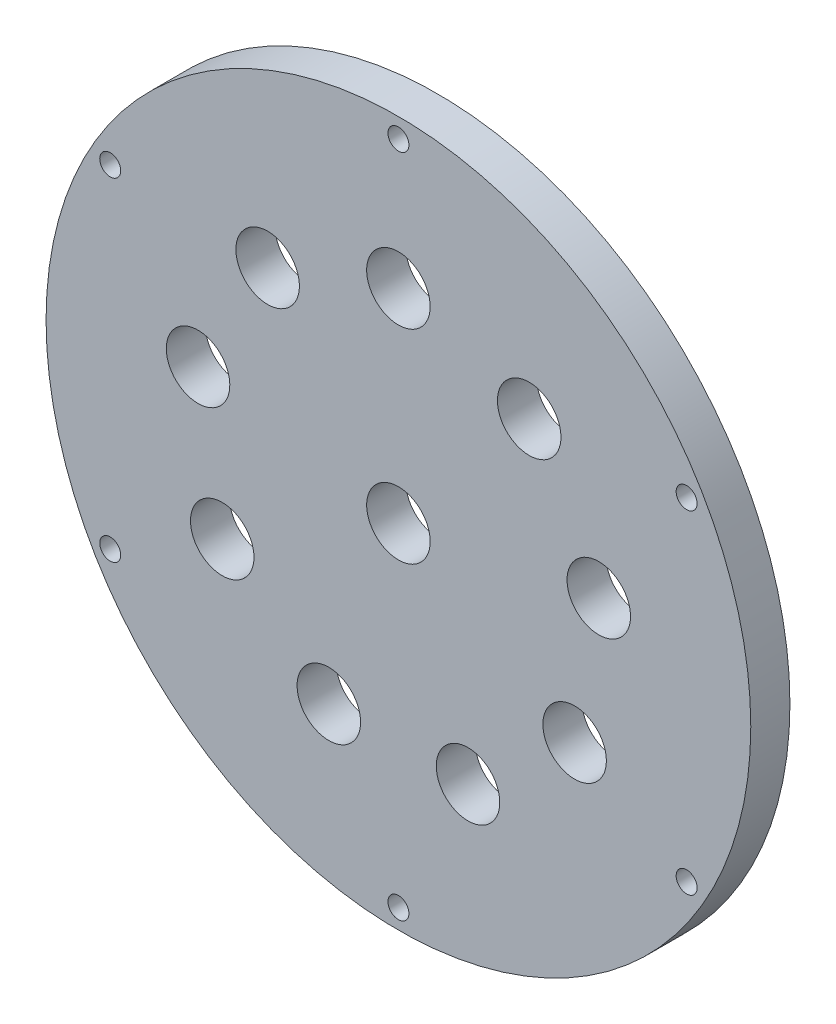
SolidWorks part; units mm, degrees
ref_plane "Front Plane" through (0, 0, 0) normal (0, 0, 1) x (1, 0, 0)
ref_plane "Top Plane" through (0, 0, 0) normal (0, 1, 0) x (1, 0, 0)
ref_plane "Right Plane" through (0, 0, 0) normal (1, 0, 0) x (0, 0, -1)
sketch "Sketch2" plane through (0, 0, 0) normal (0, 0, 1) x (1, 0, 0)
  circle A0 centre (0, 0) radius 57.15
  dimension "D1" = 114.3
extrude "Boss-Extrude1" add sketch "Sketch2" along normal blind 6.35
sketch "Sketch3" plane through (0, 0, 6.35) normal (0, 0, 1) x (1, 0, 0)
  line L0 (0, 0) -> (0, 33) construction
  circle A0 centre (0, 33) radius 5.15
  dimension "D1" = 10.3
  dimension "D2" = 33
extrude "Cut-Extrude1" cut sketch "Sketch3" against normal through all
pattern_circular "CirPattern1" count 9 over 360 about axis through (0, 0, 0) along (0, 0, 1) of "Cut-Extrude1"
sketch "Sketch6" plane through (0, 0, 6.35) normal (0, 0, 1) x (1, 0, 0)
  line L0 (0, -53.975) -> (0, 53.975) construction
  line L1 (0, 0) -> (57.15, 0) construction
  circle A0 centre (0, 53.975) radius 1.7
  circle A1 centre (0, 0) radius 57.15 construction
  dimension "D2" = 3.4
  dimension "D1" = 107.95
extrude "Cut-Extrude4" cut sketch "Sketch6" against normal through all
pattern_circular "CirPattern3" count 6 over 360 about axis through (0, 0, 0) along (0, 0, 1) of "Cut-Extrude4"
sketch "Sketch7" plane through (0, 0, 6.35) normal (0, 0, 1) x (1, 0, 0)
  line L0 (-21.212, 25.2795) -> (0, 33) construction
  line L1 (0, 33) -> (0, 0) construction
  line L2 (0, 0) -> (-10.606, 29.1397) construction
  line L3 (0, 0) -> (0, -31.0099) construction
  line L4 (-11.2867, -31.0099) -> (11.2867, -31.0099) construction
  circle A1 centre (0, 0) radius 5.15
  circle A2 centre (28.5788, -16.5) radius 5.15 construction
  point P8 (0, -0.7615)
extrude "Cut-Extrude5" cut sketch "Sketch7" against normal through all
